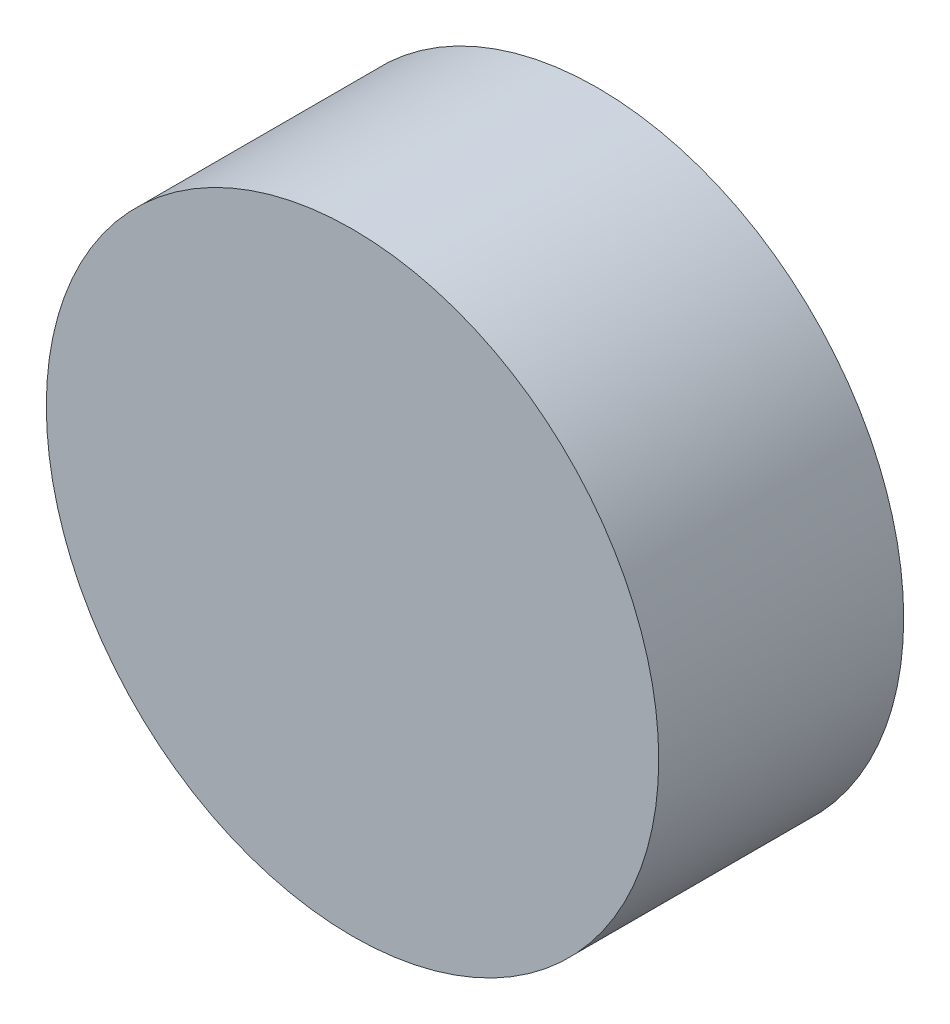
SolidWorks part; units mm, degrees
material "Hexcel AS4C (3000 Filaments)"
ref_plane "Front Plane" through (0, 0, 0) normal (0, 0, 1) x (1, 0, 0)
ref_plane "Top Plane" through (0, 0, 0) normal (0, 1, 0) x (1, 0, 0)
ref_plane "Right Plane" through (0, 0, 0) normal (1, 0, 0) x (0, 0, -1)
sketch "Sketch1" plane through (0, 0, 0) normal (0, 0, 1) x (1, 0, 0)
  circle A0 centre (0, 0) radius 12.5
  dimension "D1" = 25
extrude "Boss-Extrude1" add sketch "Sketch1" along normal blind 10
